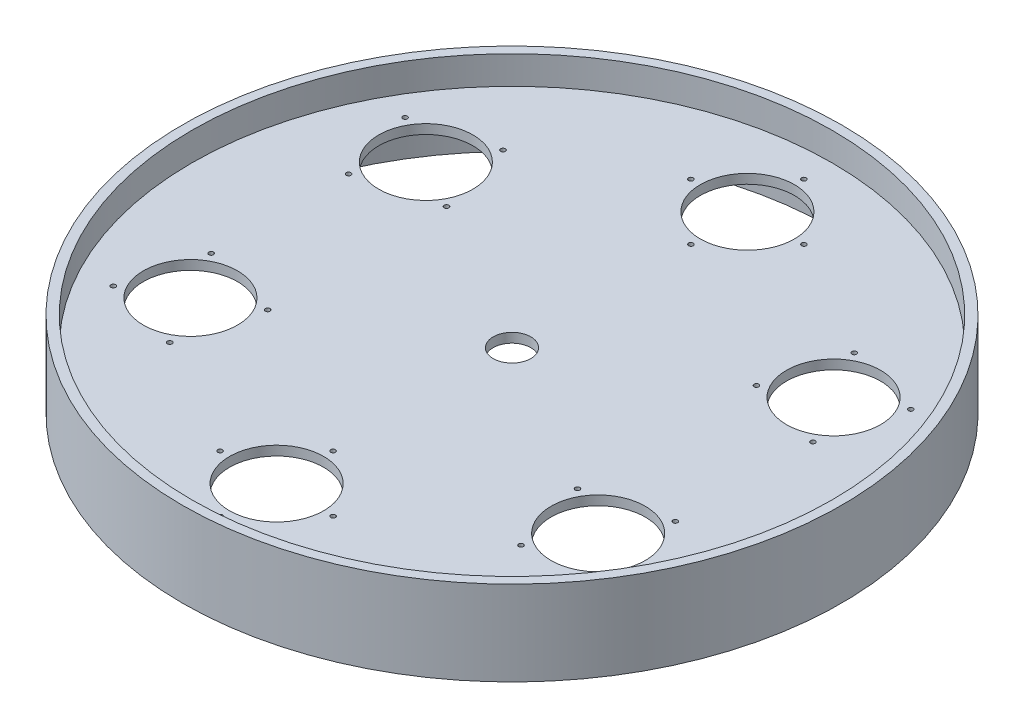
SolidWorks part; units mm, degrees
other "Marca1"
sketch "Croquis3" plane through (500, 60, 500) normal (0.4698, 0.473, 0.7453) x (0.8816, -0.2081, -0.4237)
material "AISI 316 Chapa de acero inoxidable (SS)"
ref_plane "Alzado" through (0, 0, 0) normal (0, 0, 1) x (1, 0, 0)
ref_plane "Planta" through (0, 0, 0) normal (0, 1, 0) x (1, 0, 0)
ref_plane "Vista lateral" through (0, 0, 0) normal (1, 0, 0) x (0, 0, -1)
sketch "Croquis1" plane through (0, 0, 0) normal (0, 1, 0) x (1, 0, 0)
  circle A0 centre (0, 0) radius 350
  circle A1 centre (0, 0) radius 250 construction
  circle A2 centre (0, 250) radius 50
  circle A3 centre (0, 0) radius 250 construction
  circle A5 centre (0, 0) radius 250 construction
  circle A7 centre (0, 0) radius 250 construction
  circle A9 centre (0, 0) radius 250 construction
  circle A11 centre (0, 0) radius 250 construction
  circle A13 centre (0, 0) radius 250 construction
  circle A15 centre (195.4579, 155.8725) radius 50 [skipped]
  circle A16 centre (243.732, -55.6302) radius 50 [skipped]
  circle A17 centre (108.4709, -225.2422) radius 50 [skipped]
  circle A18 centre (-108.4709, -225.2422) radius 50 [skipped]
  circle A19 centre (-243.732, -55.6302) radius 50 [skipped]
  circle A20 centre (-195.4579, 155.8725) radius 50 [skipped]
  circle A21 centre (216.5064, 125) radius 50
  circle A22 centre (216.5064, -125) radius 50
  circle A23 centre (0, -250) radius 50
  circle A24 centre (-216.5064, -125) radius 50
  circle A25 centre (-216.5064, 125) radius 50
  circle A26 centre (0, 0) radius 20
  point P23 (0, 0)
  point P27 (0, 0)
  dimension "D1" = 700
  dimension "D2" = 500
  dimension "D3" = 100
  dimension "D6" = 40
  dimension "D4" = 7
  dimension "D5" = 6
extrude "Saliente-Extruir1" add sketch "Croquis1" along normal blind 10
sketch "Croquis2" plane through (0, 0, 0) normal (0, 1, 0) x (1, 0, 0)
  circle A0 centre (0, 0) radius 350 construction
  circle A1 centre (0, 0) radius 350
  circle A2 centre (0, 0) radius 340
  dimension "D1" = 680
extrude "Saliente-Extruir2" add sketch "Croquis2" along normal blind 40 and the other way blind 50
sketch "Croquis5" plane through (0, 10, 0) normal (0, 1, 0) x (1, 0, 0)
  circle A0 centre (0, 250) radius 50 construction
  circle A1 centre (0, 250) radius 50
  circle A2 centre (0, 250) radius 60 construction
  circle A3 centre (0, 0) radius 250 construction
  circle A4 centre (0, 310) radius 2.5
  circle A5 centre (60, 250) radius 2.5
  circle A6 centre (0, 190) radius 2.5
  circle A7 centre (-60, 250) radius 2.5
  circle A8 centre (268.4679, 155) radius 2.5
  circle A9 centre (186.5064, 176.9615) radius 2.5
  circle A10 centre (246.5064, 73.0385) radius 2.5
  circle A11 centre (164.5448, 95) radius 2.5
  circle A12 centre (268.4679, -155) radius 2.5
  circle A13 centre (246.5064, -73.0385) radius 2.5
  circle A14 centre (186.5064, -176.9615) radius 2.5
  circle A15 centre (164.5448, -95) radius 2.5
  circle A16 centre (0, -310) radius 2.5
  circle A17 centre (60, -250) radius 2.5
  circle A18 centre (-60, -250) radius 2.5
  circle A19 centre (0, -190) radius 2.5
  circle A20 centre (-268.4679, -155) radius 2.5
  circle A21 centre (-186.5064, -176.9615) radius 2.5
  circle A22 centre (-246.5064, -73.0385) radius 2.5
  circle A23 centre (-164.5448, -95) radius 2.5
  circle A24 centre (-268.4679, 155) radius 2.5
  circle A25 centre (-246.5064, 73.0385) radius 2.5
  circle A26 centre (-186.5064, 176.9615) radius 2.5
  circle A27 centre (-164.5448, 95) radius 2.5
  point P18 (0, 250)
  point P59 (0, 0)
  dimension "D1" = 120
  dimension "D2" = 5
  dimension "D3" = 4
extrude "Cortar-Extruir3" cut sketch "Croquis5" against normal up to next (10 mm away)
